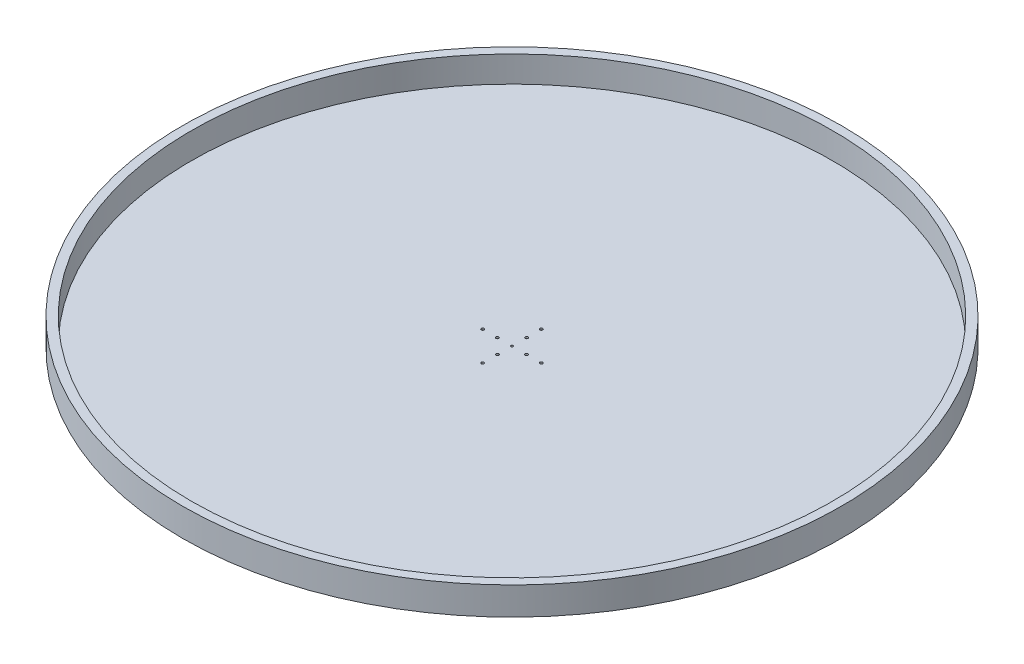
SolidWorks part; units mm, degrees
ref_plane "Front Plane" through (0, 0, 0) normal (0, 0, 1) x (1, 0, 0)
ref_plane "Top Plane" through (0, 0, 0) normal (0, 1, 0) x (1, 0, 0)
ref_plane "Right Plane" through (0, 0, 0) normal (1, 0, 0) x (0, 0, -1)
sketch "Sketch1" plane through (0, 0, 0) normal (0, 1, 0) x (1, 0, 0)
  circle A0 centre (0, 0) radius 472.5
  dimension "D1" = 945
extrude "Boss-Extrude1" add sketch "Sketch1" along normal blind 40
sketch "Sketch3" plane through (0, 40, 0) normal (0, 1, 0) x (1, 0, 0)
  circle A0 centre (0, 0) radius 460
  dimension "D1" = 920
extrude "Cut-Extrude1" cut sketch "Sketch3" against normal blind 37.46
sketch "Sketch5" plane through (0, 2.54, 0) normal (0, 1, 0) x (1, 0, 0)
  circle A0 centre (0, 0) radius 1.5
  dimension "D1" = 3
sketch "Sketch4" [suppressed] plane through (0, 0, 0) normal (0, -1, 0) x (1, 0, 0)
  line L0 (22, 0) -> (-22, 0) construction
  line L1 (-381, 12.7) -> (-12.7, 12.7)
  line L2 (-381, 12.7) -> (-381, -12.7)
  line L3 (-381, -12.7) -> (-12.7, -12.7)
  line L4 (381, 12.7) -> (381, -12.7)
  line L5 (-381, 12.7) -> (381, -12.7) construction
  line L6 (-381, -12.7) -> (381, 12.7) construction
  line L7 (0, -22) -> (0, 22) construction
  line L8 (-12.7, -12.7) -> (-12.7, -381)
  line L9 (12.7, 381) -> (-12.7, 381)
  line L10 (12.7, 381) -> (12.7, 12.7)
  line L11 (12.7, -381) -> (-12.7, -381)
  line L12 (-12.7, 381) -> (-12.7, 12.7)
  line L13 (12.7, 381) -> (-12.7, -381) construction
  line L14 (12.7, -381) -> (-12.7, 381) construction
  line L15 (-12.7, 0.4233) -> (-12.7, -0.4233)
  line L16 (-0.4233, 12.7) -> (0.4233, 12.7)
  line L17 (12.7, 12.7) -> (381, 12.7)
  line L18 (12.7, 0.4233) -> (12.7, -0.4233)
  line L19 (12.7, -12.7) -> (12.7, -381)
  line L20 (12.7, -12.7) -> (381, -12.7)
  line L21 (-0.4233, -12.7) -> (0.4233, -12.7)
  point P0 (0, 0)
  point P9 (0, 0)
  dimension "D1" = 12.7
  dimension "D2" = 12.7
  dimension "D3" = 381
  dimension "D4" = 381
  dimension "D5" = 12.7
  dimension "D6" = 12.7
  dimension "D7" = 381
  dimension "D8" = 381
extrude "Cut-Extrude3" cut sketch "Sketch5" against normal through all
sketch "Sketch8" plane through (0, 2.54, 0) normal (0, 1, 0) x (1, 0, 0)
  circle A0 centre (0, 42) radius 2.02
  circle A1 centre (0, 0) radius 1.5 construction
  circle A2 centre (42, 0) radius 2.02
  circle A3 centre (0, -42) radius 2.02
  circle A4 centre (-42, 0) radius 2.02
  circle A5 centre (0, 21) radius 2.02
  circle A6 centre (21, 0) radius 2.02
  circle A7 centre (0, -21) radius 2.02
  circle A8 centre (-21, 0) radius 2.02
  point P13 (0, 0)
  point P22 (0, 0)
  dimension "D1" = 4.04
  dimension "D2" = 42
  dimension "D4" = 4.04
  dimension "D5" = 21
  dimension "D3" = 4
  dimension "D6" = 4
extrude "Cut-Extrude4" cut sketch "Sketch8" against normal through all
